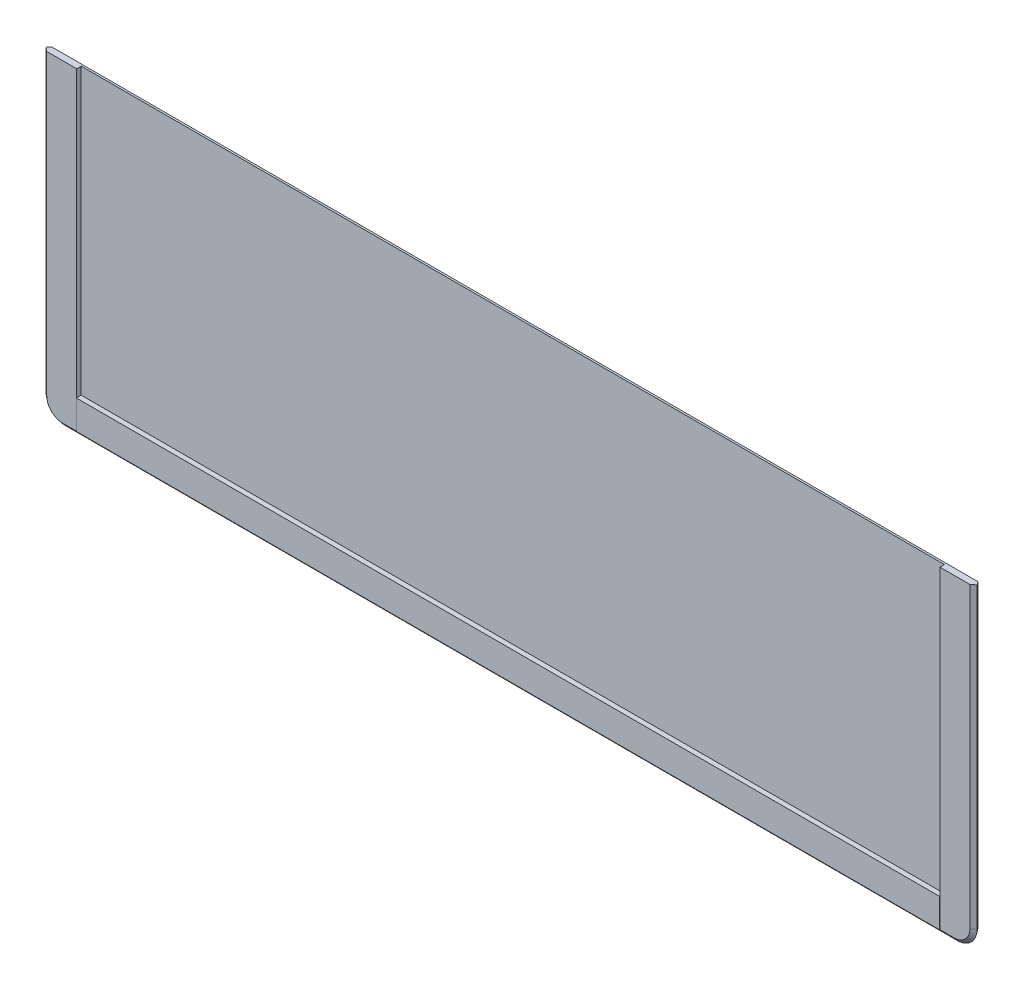
SolidWorks part; units mm, degrees
ref_plane "Plan de face" through (0, 0, 0) normal (0, 0, 1) x (1, 0, 0)
ref_plane "Plan de dessus" through (0, 0, 0) normal (0, 1, 0) x (1, 0, 0)
ref_plane "Plan de droite" through (0, 0, 0) normal (1, 0, 0) x (0, 0, -1)
sketch "Esquisse1" plane through (0, 0, 0) normal (0, 0, 1) x (1, 0, 0)
  line L0 (-154.4511, 0.2) -> (-154.4511, -92.3) construction
  line L5 (-146.4511, -100.3) -> (129.5489, -100.3) construction
  line L6 (137.5489, -92.3) -> (137.5489, 0.2) construction
  line L7 (-154.4511, 0) -> (-154.4511, -92.3)
  line L8 (-146.4511, -100.3) -> (129.5489, -100.3)
  line L9 (137.5489, -92.3) -> (137.5489, 0)
  line L13 (137.5489, 0) -> (-154.4511, 0)
  arc A0 (-154.4511, -92.3) -> (-146.4511, -100.3) centre (-146.4511, -92.3) ccw construction
  arc A1 (129.5489, -100.3) -> (137.5489, -92.3) centre (129.5489, -92.3) ccw construction
  arc A2 (-154.4511, -92.3) -> (-146.4511, -100.3) centre (-146.4511, -92.3) ccw
  arc A3 (129.5489, -100.3) -> (137.5489, -92.3) centre (129.5489, -92.3) ccw
extrude "Boss.-Extru.1" add sketch "Esquisse1" along normal blind 2
sketch "Esquisse3" plane through (0, 0, 0) normal (0, 0, -1) x (-1, 0, 0)
  line L0 (154.4511, 0.2) -> (154.4511, -92.3) construction
  line L1 (146.4511, -100.3) -> (-129.5489, -100.3) construction
  line L2 (-137.5489, -92.3) -> (-137.5489, 0.2) construction
  line L3 (154.4511, 0.2) -> (154.4511, -92.3)
  line L4 (146.4511, -100.3) -> (-129.5489, -100.3)
  line L5 (-137.5489, -92.3) -> (-137.5489, 0.2)
  arc A0 (146.4511, -100.3) -> (154.4511, -92.3) centre (146.4511, -92.3) ccw construction
  arc A1 (-137.5489, -92.3) -> (-129.5489, -100.3) centre (-129.5489, -92.3) ccw construction
  arc A2 (146.4511, -100.3) -> (154.4511, -92.3) centre (146.4511, -92.3) ccw
  arc A3 (-137.5489, -92.3) -> (-129.5489, -100.3) centre (-129.5489, -92.3) ccw
sketch "Esquisse4" plane through (0, 0, 0) normal (0, 1, 0) x (1, 0, 0)
  line L0 (147.6731, 0) -> (134.9564, 0) construction
  line L1 (147.6731, 0) -> (134.9564, 0)
  line L2 (147.6731, -8.5) -> (147.6731, 0) construction
  line L3 (147.6731, -7.75) -> (147.6731, 0)
  line L4 (137.5489, -7.75) -> (147.6731, -7.75)
  line L5 (139.9679, -1) -> (135.6704, -1) construction
  line L6 (135.6704, -1) -> (134.4463, -2)
  line L7 (137.5489, -2) -> (-154.4511, -2) construction
  line L8 (134.4463, -2) -> (136.1826, -2)
  arc A0 (134.5935, -1.7433) -> (134.6989, -2) centre (134.6989, -1.85) ccw construction
  spline S0 degree 3 poles (407.4457, -1980.5248) (-287.9374, 2050.098) (692.1387, -2029.593) (-522.7841, 1879.1519) knots -8.704614 -8.704614 -8.704614 -8.704614 10.068975 10.068975 10.068975 10.068975 only from (134.9564, 0) to (137.5489, -7.75) construction
  spline S1 degree 3 poles (134.9564, 0) (136.3536, -1.5617) (137.4127, -4.956) (137.5489, -7.75) knots 0 0 0 0 1 1 1 1
  point P7 (134.5602, -1.907)
  dimension "D1" = 1
sketch "Esquisse9" plane through (0, 0, 0) normal (0, 1, 0) x (1, 0, 0)
  line L0 (135.6704, -1) -> (134.4463, -2) construction
  line L1 (134.4463, -2) -> (136.1826, -2) construction
  line L2 (135.6704, -1) -> (134.4463, -2)
  line L3 (147.6731, 0) -> (134.9564, 0)
  line L4 (137.5489, -7.75) -> (147.6731, -7.75)
  line L5 (147.6731, -7.75) -> (147.6731, 0)
  line L6 (147.6731, 0) -> (134.9564, 0)
  line L8 (147.6731, -2) -> (147.6731, 0)
  line L9 (134.4463, -2) -> (136.1826, -2)
  line L10 (136.1826, -2) -> (147.6731, -2)
  spline S1 degree 3 poles (244.5145, -993.9774) (-73.0293, 1052.7193) (430.3176, -1043.5282) (-219.0979, 926.4758) knots -6.816106 -6.816106 -6.816106 -6.816106 8.182474 8.182474 8.182474 8.182474 only from (134.9564, 0) to (137.5489, -7.75)
  spline S2 degree 3 poles (134.9564, 0) (135.2063, -0.2793) (135.4454, -0.6173) (135.6704, -1) knots 0 0 0 0 0.178871 0.178871 0.178871 0.178871
  dimension "D1" = 0
sweep "Enlèvement de matière-Balayage3" cut profiles "Esquisse9" path "Esquisse3"
sketch "Esquisse5" plane through (0, 0, 2) normal (0, 0, 1) x (1, 0, 0)
  line L0 (125.1704, -88.2214) -> (125.1704, 0.2)
  line L1 (125.1704, 0.2) -> (125.1704, 5.2643)
  line L2 (125.1704, 5.2643) -> (-142.0725, 5.2643)
  line L3 (-142.0725, 5.2643) -> (-142.0725, 0.2)
  line L4 (-142.0725, 0.2) -> (-142.0725, -88.2214)
  line L6 (124.927, -84.478) -> (124.927, 0.2)
  line L7 (124.927, 0.2) -> (124.927, 5.0209)
  line L8 (124.927, 5.0209) -> (-141.8291, 5.0209)
  line L9 (-141.8291, 5.0209) -> (-141.8291, 0.2)
  line L10 (-141.8291, 0.2) -> (-141.8291, -84.478)
  line L11 (-138.8291, -87.478) -> (121.927, -87.478)
  line L12 (124.927, -84.478) -> (124.927, 0.2)
  line L13 (124.927, 0.2) -> (124.927, 5.0209)
  line L14 (124.927, 5.0209) -> (-141.8291, 5.0209)
  line L15 (-141.8291, 5.0209) -> (-141.8291, 0.2)
  line L16 (-141.8291, 0.2) -> (-141.8291, -84.478)
  line L17 (-138.8291, -87.478) -> (121.927, -87.478)
  line L18 (-138.8291, -87.7214) -> (121.927, -87.7214) construction
  line L19 (125.1704, -84.478) -> (125.1704, 0.2) construction
  line L21 (-142.0725, 0.2) -> (-142.0725, -84.478) construction
  line L22 (135.6704, 0) -> (135.6704, -92.3) construction
  line L23 (-142.0725, -88.2214) -> (125.1704, -88.2214)
  line L24 (129.5489, -98.4214) -> (-146.4511, -98.4214) construction
  arc A2 (121.927, -87.478) -> (124.927, -84.478) centre (121.927, -84.478) ccw
  arc A3 (-141.8291, -84.478) -> (-138.8291, -87.478) centre (-138.8291, -84.478) ccw
  arc A4 (121.927, -87.478) -> (124.927, -84.478) centre (121.927, -84.478) ccw
  arc A5 (-141.8291, -84.478) -> (-138.8291, -87.478) centre (-138.8291, -84.478) ccw
  arc A6 (121.927, -87.7214) -> (125.1704, -84.478) centre (121.927, -84.478) ccw construction
  arc A7 (-142.0725, -84.478) -> (-138.8291, -87.7214) centre (-138.8291, -84.478) ccw construction
  dimension "D2" = 10.5
  dimension "D3" = 10.2
  dimension "D1" = 0
extrude "Enlèv. mat.-Extru.1" cut sketch "Esquisse5" against normal blind 1.4
sketch "Esquisse10" plane through (0, 0, 2) normal (0, 0, 1) x (1, 0, 0)
  line L0 (129.5489, -97.1973) -> (-146.4511, -97.1973) construction
  line L1 (125.1704, -88.2214) -> (-142.0725, -88.2214)
  line L2 (125.1704, -88.2214) -> (125.1704, -97.1973)
  line L3 (125.1704, -97.1973) -> (-142.0725, -97.1973)
  line L4 (-142.0725, -88.2214) -> (-142.0725, -97.1973)
extrude "Boss.-Extru.3" add sketch "Esquisse10" along normal blind 0.1
sketch "Esquisse11" plane through (0, 0, 0) normal (0, 0, -1) x (-1, 0, 0)
  line L0 (7.7511, -61.9214) -> (7.7511, -49.4214)
  line L1 (-4.7489, -35.5214) -> (7.7511, -35.5214)
  line L2 (-4.7489, -35.5214) -> (-4.7489, -48.0214)
  line L3 (-4.7489, -61.9214) -> (7.7511, -61.9214)
  line L4 (21.6511, -35.5214) -> (21.6511, -48.0214)
  line L5 (-4.7489, -49.4214) -> (7.7511, -49.4214)
  line L6 (21.6511, -48.0214) -> (9.1511, -48.0214)
  line L7 (9.1511, -35.5214) -> (9.1511, -48.0214)
  line L8 (9.1511, -61.9214) -> (21.6511, -61.9214)
  line L9 (9.1511, -49.4214) -> (21.6511, -49.4214)
  line L10 (7.7511, -48.0214) -> (7.7511, -35.5214)
  line L11 (-4.7489, -49.4214) -> (-4.7489, -61.9214)
  line L12 (7.7511, -48.0214) -> (-4.7489, -48.0214)
  line L13 (9.1511, -35.5214) -> (21.6511, -35.5214)
  line L14 (9.1511, -49.4214) -> (9.1511, -61.9214)
  line L15 (21.6511, -49.4214) -> (21.6511, -61.9214)
  line L16 (7.7511, -35.5214) -> (9.1511, -35.5214) construction
  line L17 (-4.7489, -49.4214) -> (-4.7489, -48.0214) construction
  line L18 (-4.7489, -48.7214) -> (21.6511, -48.7214) construction
  line L19 (8.4511, -35.5214) -> (8.4511, -61.9214) construction
  line L20 (7.7511, -61.9214) -> (9.1511, -61.9214) construction
  line L21 (21.6511, -48.0214) -> (21.6511, -49.4214) construction
  line L22 (-129.5489, -98.4214) -> (146.4511, -98.4214) construction
  line L24 (8.4511, 0) -> (8.4511, -35.5214) construction
  line L25 (-134.9564, 0) -> (151.8586, 0) construction
  point P20 (8.4511, -48.7214)
  dimension "D1" = 1.4
  dimension "D2" = 26.4
  dimension "D3" = 36.5
extrude "Enlèv. mat.-Extru.2" cut sketch "Esquisse11" against normal blind 0.1
